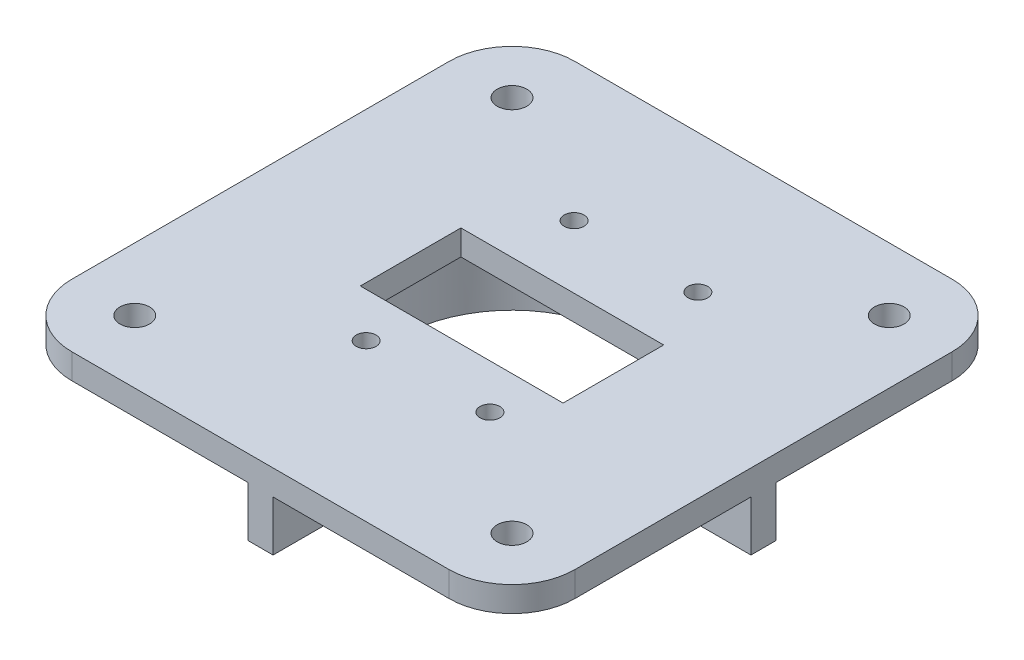
SolidWorks part; units mm, degrees
ref_plane "Front Plane" through (0, 0, 0) normal (0, 0, 1) x (1, 0, 0)
ref_plane "Top Plane" through (0, 0, 0) normal (0, 1, 0) x (1, 0, 0)
ref_plane "Right Plane" through (0, 0, 0) normal (1, 0, 0) x (0, 0, -1)
sketch "Sketch1" plane through (0, 0, 0) normal (0, 1, 0) x (1, 0, 0)
  line L1 (6.35, 0) -> (44.45, 0)
  line L2 (0, 6.35) -> (0, 44.45)
  line L3 (6.35, 50.8) -> (44.45, 50.8)
  line L4 (50.8, 6.35) -> (50.8, 44.45)
  line L5 (6.35, 44.45) -> (44.45, 44.45) construction
  line L6 (6.35, 44.45) -> (6.35, 6.35) construction
  line L7 (6.35, 6.35) -> (44.45, 6.35) construction
  line L8 (44.45, 44.45) -> (44.45, 6.35) construction
  arc A0 (44.45, 0) -> (50.8, 6.35) centre (44.45, 6.35) ccw
  arc A1 (44.45, 50.8) -> (50.8, 44.45) centre (44.45, 44.45) cw
  arc A2 (0, 44.45) -> (6.35, 50.8) centre (6.35, 44.45) cw
  arc A3 (6.35, 0) -> (0, 6.35) centre (6.35, 6.35) cw
  circle A4 centre (6.35, 6.35) radius 1.5
  circle A5 centre (6.35, 44.45) radius 1.5
  circle A6 centre (44.45, 44.45) radius 1.5
  circle A7 centre (44.45, 6.35) radius 1.5
  circle A8 centre (25.4, 25.4) radius 11.43
  point P13 (50.8, 50.8)
  point P16 (0, 50.8)
  point P19 (0, 0)
  dimension "D6" = 6.35
  dimension "D7" = 3
  dimension "D10" = 22.86
  dimension "D1" = 50.8
  dimension "D2" = 50.8
  dimension "D3" = 6.35
  dimension "D4" = 6.35
  dimension "D5" = 6.35
  dimension "D8" = 25.4
  dimension "D9" = 25.4
extrude "Boss-Extrude1" add sketch "Sketch1" along normal blind 7.62
sketch "Sketch2" plane through (0, 0, 0) normal (0, -1, 0) x (1, 0, 0)
  line L0 (0, -44.45) -> (0, -6.35) construction
  line L1 (0, -26.67) -> (50.8, -26.67)
  line L2 (0, -26.67) -> (0, -24.13)
  line L3 (0, -24.13) -> (50.8, -24.13)
  line L4 (50.8, -26.67) -> (50.8, -24.13)
  line L5 (50.8, -6.35) -> (50.8, -44.45) construction
  line L6 (6.35, 0) -> (44.45, 0) construction
  line L7 (26.67, 0) -> (24.13, 0)
  line L8 (26.67, 0) -> (26.67, -50.8)
  line L9 (26.67, -50.8) -> (24.13, -50.8)
  line L10 (24.13, 0) -> (24.13, -50.8)
  line L11 (44.45, -50.8) -> (6.35, -50.8) construction
  line L13 (0, -50.8) -> (50.8, -50.8)
  line L14 (0, -50.8) -> (0, 0)
  line L15 (0, 0) -> (50.8, 0)
  line L16 (50.8, -50.8) -> (50.8, 0)
  circle A0 centre (25.4, -25.4) radius 16.51
  arc M10 (50.8, -6.35) -> (44.45, 0) centre (44.45, -6.35) ccw
  line M11 (44.45, 0) -> (6.35, 0)
  arc M12 (6.35, 0) -> (0, -6.35) centre (6.35, -6.35) ccw
  line M13 (0, -6.35) -> (0, -44.45)
  arc M14 (0, -44.45) -> (6.35, -50.8) centre (6.35, -44.45) ccw
  line M15 (6.35, -50.8) -> (44.45, -50.8)
  arc M16 (44.45, -50.8) -> (50.8, -44.45) centre (44.45, -44.45) ccw
  line M17 (50.8, -44.45) -> (50.8, -6.35)
  circle M18 centre (6.35, -6.35) radius 1.5
  circle M19 centre (6.35, -44.45) radius 1.5
  circle M20 centre (44.45, -44.45) radius 1.5
  circle M21 centre (44.45, -6.35) radius 1.5
  dimension "D1" = 33.02
  dimension "D2" = 2.54
  dimension "D3" = 2.54
  dimension "D4" = 24.13
  dimension "D5" = 24.13
extrude "Cut-Extrude1" cut sketch "Sketch2" against normal blind 5.08 contours A0 L1 L10 M13 M14 M15 M19 | A0 L10 L3 M11 M12 M13 M18 | A0 L3 L8 M17 M10 M11 M21 | A0 L8 L1 M15 M16 M17 M20 | L14 L15 L16 L13
sketch "Sketch3" plane through (0, 7.62, 0) normal (0, 1, 0) x (1, 0, 0)
  line L1 (15.1609, 20.32) -> (35.6391, 20.32)
  line L2 (15.1609, 20.32) -> (15.1609, 30.48)
  line L3 (15.1609, 30.48) -> (35.6391, 30.48)
  line L4 (35.6391, 20.32) -> (35.6391, 30.48)
  circle A0 centre (25.4, 25.4) radius 11.43 construction
  circle A1 centre (25.4, 25.4) radius 11.43
  circle M17 centre (25.4, 25.4) radius 11.43
  dimension "D1" = 10.16
extrude "Boss-Extrude2" add sketch "Sketch3" against normal blind 2.54 contours L1 M17 | L2 M17 | L3 M17 | L4 M17
sketch "Sketch4" plane through (0, 7.62, 0) normal (0, 1, 0) x (1, 0, 0)
  line L0 (15.1609, 20.32) -> (15.1609, 30.48) construction
  line L1 (15.1609, 30.48) -> (35.6391, 30.48) construction
  circle A0 centre (20.2409, 36.83) radius 1
  circle A1 centre (32.7409, 36.83) radius 1
  circle A2 centre (20.2409, 15.83) radius 1
  circle A3 centre (32.7409, 15.83) radius 1
  dimension "D2" = 12.5
  dimension "D5" = 2
  dimension "D1" = 21
  dimension "D3" = 5.08
  dimension "D4" = 6.35
extrude "Cut-Extrude2" cut sketch "Sketch4" against normal through all
